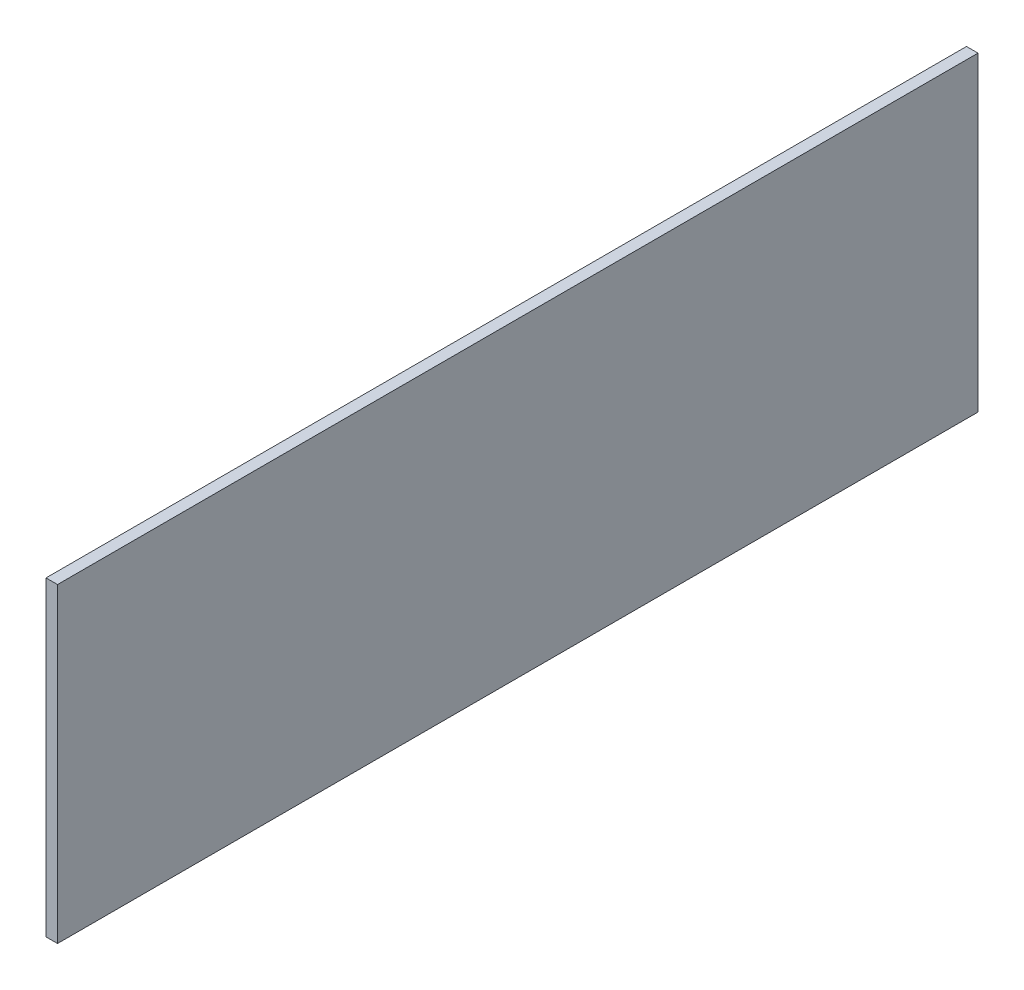
SolidWorks part; units mm, degrees
material "Pine"
ref_plane "Front Plane" through (0, 0, 0) normal (0, 0, 1) x (1, 0, 0)
ref_plane "Top Plane" through (0, 0, 0) normal (0, 1, 0) x (1, 0, 0)
ref_plane "Right Plane" through (0, 0, 0) normal (1, 0, 0) x (0, 0, -1)
sketch "Sketch1" plane through (0, 0, 0) normal (1, 0, 0) x (0, 0, -1)
  line L1 (508, 171.577) -> (-508, 171.577)
  line L2 (508, 171.577) -> (508, -171.577)
  line L3 (508, -171.577) -> (-508, -171.577)
  line L4 (-508, 171.577) -> (-508, -171.577)
  line L5 (508, 171.577) -> (-508, -171.577) construction
  line L6 (508, -171.577) -> (-508, 171.577) construction
  point P0 (0, 0)
  dimension "D1" = 343.154
  dimension "D2" = 1016
extrude "Boss-Extrude1" add sketch "Sketch1" along normal blind 12.7
